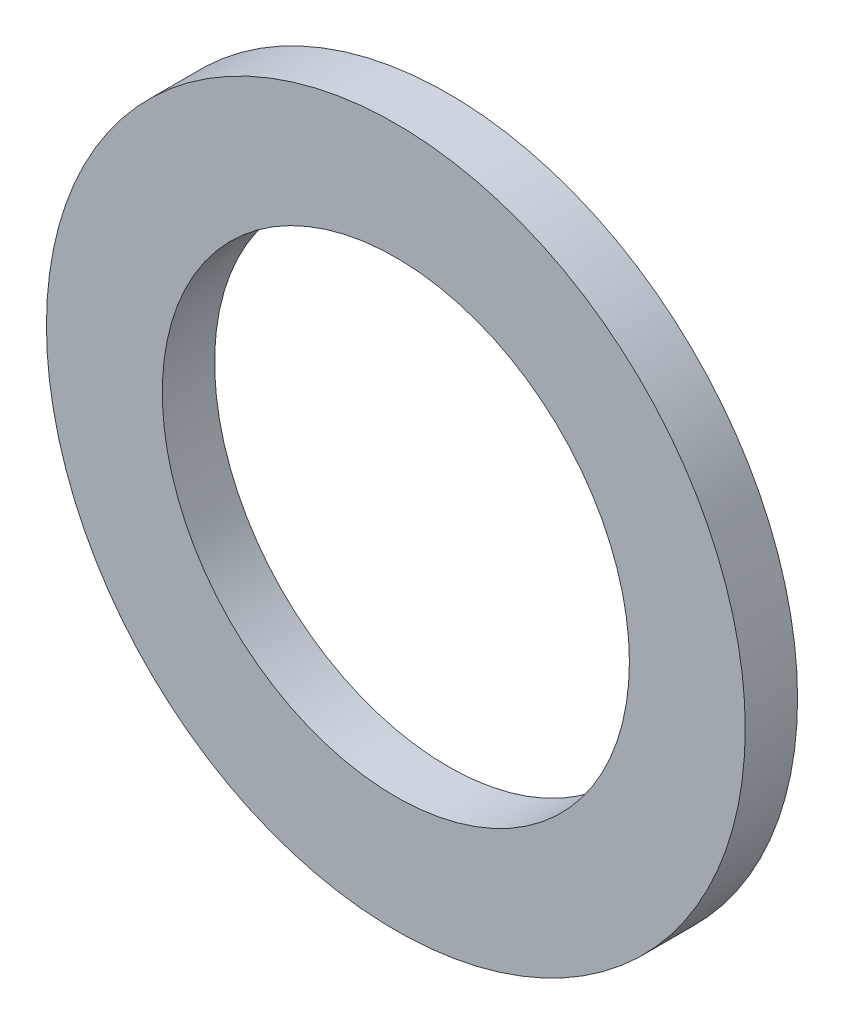
SolidWorks part; units mm, degrees
material "6061 Alloy"
ref_plane "Front Plane" through (0, 0, 0) normal (0, 0, 1) x (1, 0, 0)
ref_plane "Top Plane" through (0, 0, 0) normal (0, 1, 0) x (1, 0, 0)
ref_plane "Right Plane" through (0, 0, 0) normal (1, 0, 0) x (0, 0, -1)
sketch "Sketch1" plane through (0, 0, 0) normal (0, 0, 1) x (1, 0, 0)
  circle A0 centre (0, 0) radius 1.5875
  circle A1 centre (0, 0) radius 2.3749
  dimension "D1" = 3.175
  dimension "D2" = 4.7498
extrude "Boss-Extrude1" add sketch "Sketch1" along normal blind 0.3556
